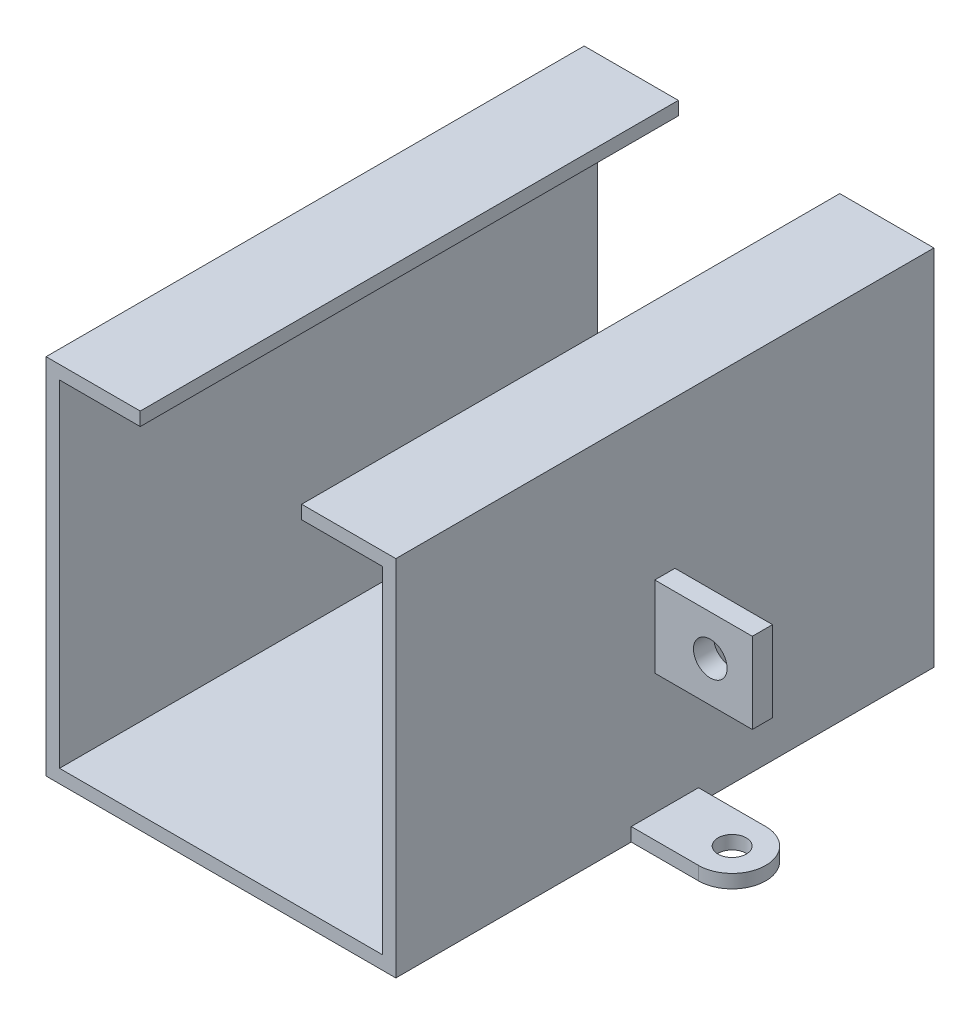
SolidWorks part; units mm, degrees
material "ABS PC"
ref_plane "Front Plane" through (0, 0, 0) normal (0, 0, 1) x (1, 0, 0)
ref_plane "Top Plane" through (0, 0, 0) normal (0, 1, 0) x (1, 0, 0)
ref_plane "Right Plane" through (0, 0, 0) normal (1, 0, 0) x (0, 0, -1)
sketch "Sketch1" plane through (0, 0, 0) normal (0, 0, 1) x (1, 0, 0)
  line L0 (0, 0) -> (0, 50)
  line L1 (0, 0) -> (48, 0)
  line L2 (48, 0) -> (48, 50)
  line L3 (0, 50) -> (12, 50)
  line L4 (48, 50) -> (36, 50)
  line L6 (-2, 25) -> (-2, -2)
  line L7 (-2, 25) -> (-2, 52)
  line L8 (-2, 52) -> (12, 52)
  line L9 (12, 52) -> (12, 50)
  line L10 (-2, -2) -> (50, -2)
  line L11 (50, -2) -> (50, 52)
  line L12 (50, 52) -> (36, 52)
  line L13 (36, 52) -> (36, 50)
  dimension "D3" = 12
  dimension "D1" = 50
  dimension "D2" = 48
  dimension "D4" = 12
  dimension "D5" = 2
  dimension "D6" = 27
  dimension "D7" = 27
  dimension "D8" = 52
  dimension "D9" = 54
  dimension "D10" = 50
extrude "Boss-Extrude1" add sketch "Sketch1" along normal blind 80
sketch "Sketch2" plane through (0, -2, 0) normal (0, -1, 0) x (1, 0, 0)
  line L1 (50, 80) -> (50, 0) construction
  line L3 (50, 45) -> (60, 45)
  line L4 (50, 35) -> (60, 35)
  line L5 (50, 45) -> (50, 35)
  line L6 (50, 45) -> (-2, 45)
  line L7 (-2, 80) -> (-2, 0) construction
  line L8 (-2, 45) -> (-2, 35)
  line L9 (-2, 35) -> (-12, 35)
  line L10 (-2, 45) -> (-12, 45)
  arc A0 (60, 45) -> (60, 35) centre (60, 40) cw
  circle A1 centre (60, 40) radius 2.1
  arc A2 (-12, 35) -> (-12, 45) centre (-12, 40) cw
  circle A3 centre (-12, 40) radius 2.1
  line M9 (50, 0) -> (50, 80)
  line M11 (-2, 80) -> (-2, 0)
  dimension "D4" = 4.2
  dimension "D6" = 4.2
  dimension "D3" = 10
  dimension "D5" = 10
extrude "Boss-Extrude2" add sketch "Sketch2" against normal blind 2 contours A0 L3 L4 A1 M9 | A2 L9 L10 A3 M11
sketch "Sketch3" plane through (-2, 0, 0) normal (-1, 0, 0) x (0, 0, 1)
  line L0 (80, 25) -> (41.5, 25)
  line L2 (80, 52) -> (80, -2) construction
  line L3 (41.5, 25) -> (38.5, 25)
  line L4 (38.5, 25) -> (38.5, 30)
  line L5 (38.5, 25) -> (38.5, 18)
  line L6 (38.5, 30) -> (41.5, 30)
  line L7 (41.5, 30) -> (41.5, 18)
  line L8 (41.5, 18) -> (38.5, 18)
  dimension "D1" = 38.5
  dimension "D2" = 3
  dimension "D3" = 5
  dimension "D4" = 7
extrude "Boss-Extrude3" add sketch "Sketch3" along normal blind 14.5 contours L7 L6 L4 L3 | L8 L7 L3 L5
sketch "Sketch5" plane through (50, 0, 0) normal (1, 0, 0) x (0, 0, -1)
  line L0 (-80, 25) -> (-41.5, 25)
  line L1 (-80, -2) -> (-80, 52) construction
  line L2 (-41.5, 25) -> (-38.5, 25)
  line L3 (-38.5, 25) -> (-38.5, 30)
  line L4 (-38.5, 25) -> (-38.5, 18)
  line L5 (-38.5, 30) -> (-41.5, 30)
  line L6 (-41.5, 30) -> (-41.5, 18)
  line L7 (-41.5, 18) -> (-38.5, 18)
  dimension "D1" = 38.5
  dimension "D2" = 3
  dimension "D3" = 5
  dimension "D4" = 7
extrude "Boss-Extrude4" add sketch "Sketch5" along normal blind 14.5 contours L5 L6 L2 L3 | L6 L7 L4 L2
sketch "Sketch8" plane through (0, 0, 38.5) normal (0, 0, -1) x (-1, 0, 0)
  circle A0 centre (-58.25, 24) radius 2.5
  circle A1 centre (10.25, 24) radius 2.5
extrude "Cut-Extrude1" cut sketch "Sketch8" against normal blind 10
